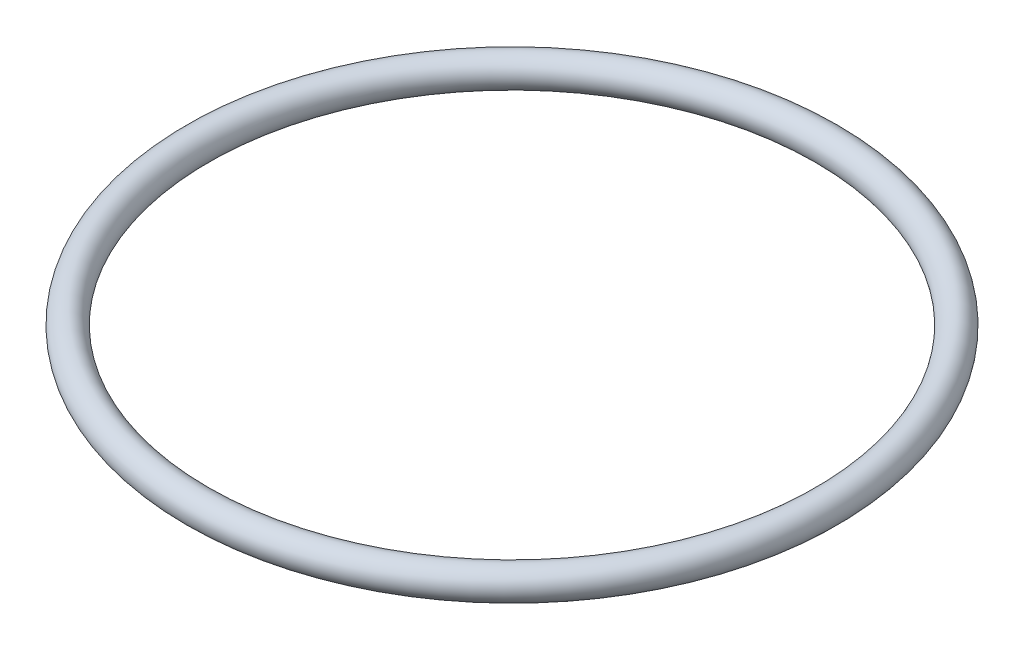
SolidWorks part; units mm, degrees
material "Natural Rubber"
ref_plane "Front Plane" through (0, 0, 0) normal (0, 0, 1) x (1, 0, 0)
ref_plane "Top Plane" through (0, 0, 0) normal (0, 1, 0) x (1, 0, 0)
ref_plane "Right Plane" through (0, 0, 0) normal (1, 0, 0) x (0, 0, -1)
sketch "Sketch1" plane through (0, 0, 0) normal (0, 0, 1) x (1, 0, 0)
  line L0 (0, 0) -> (0, 64.3129) construction
  circle A0 centre (30.75, 0) radius 1.5
  dimension "D1" = 3
  dimension "D2" = 61.5
revolve "Revolve1" add sketch "Sketch1" angle 360 about L0
